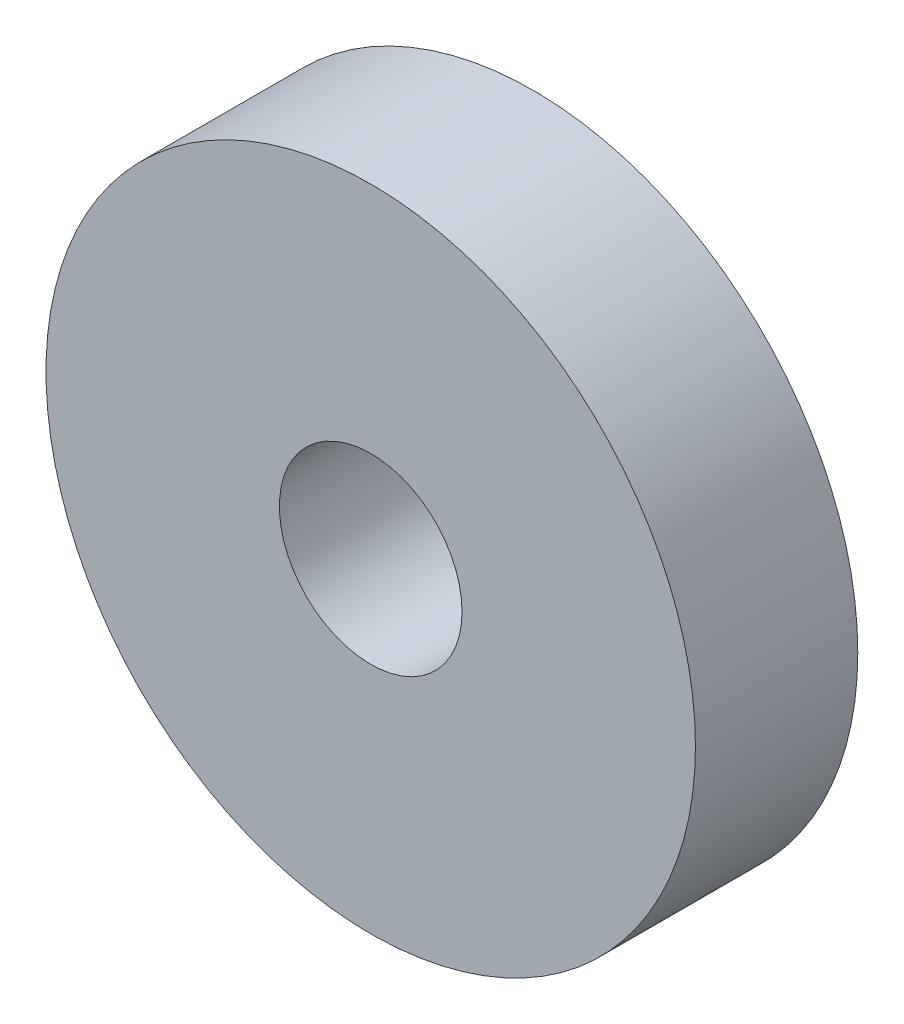
SolidWorks part; units mm, degrees
ref_plane "Front Plane" through (0, 0, 0) normal (0, 0, 1) x (1, 0, 0)
ref_plane "Top Plane" through (0, 0, 0) normal (0, 1, 0) x (1, 0, 0)
ref_plane "Right Plane" through (0, 0, 0) normal (1, 0, 0) x (0, 0, -1)
sketch "Sketch1" plane through (0, 0, 0) normal (0, 0, 1) x (1, 0, 0)
  circle A0 centre (0, 0) radius 50.8
  circle A1 centre (0, 0) radius 14.2875
  dimension "D1" = 101.6
  dimension "D2" = 28.575
extrude "Boss-Extrude1" add sketch "Sketch1" along normal blind 25.4
